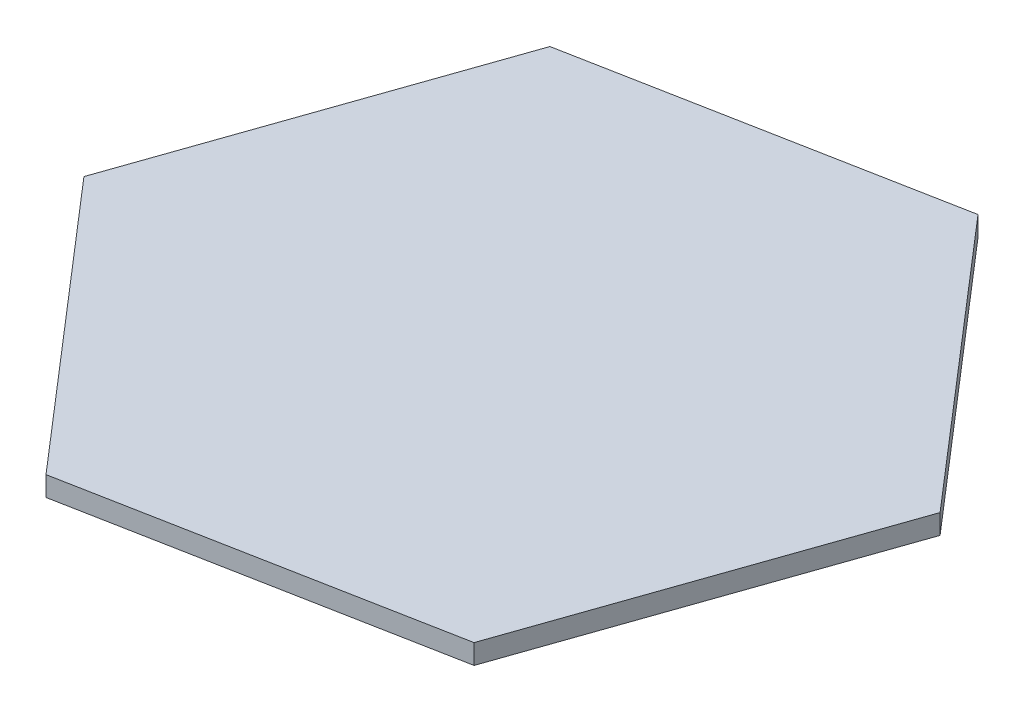
SolidWorks part; units mm, degrees
ref_plane "Front Plane" through (0, 0, 0) normal (0, 0, 1) x (1, 0, 0)
ref_plane "Top Plane" through (0, 0, 0) normal (0, 1, 0) x (1, 0, 0)
ref_plane "Right Plane" through (0, 0, 0) normal (1, 0, 0) x (0, 0, -1)
sketch "Sketch1" plane through (0, 0, 0) normal (0, 1, 0) x (1, 0, 0)
  line L1 (120.7144, -139.8592) -> (181.4788, 34.6121)
  line L2 (181.4788, 34.6121) -> (60.7644, 174.4713)
  line L3 (60.7644, 174.4713) -> (-120.7144, 139.8592)
  line L4 (-120.7144, 139.8592) -> (-181.4788, -34.6121)
  line L5 (-181.4788, -34.6121) -> (-60.7644, -174.4713)
  line L6 (-60.7644, -174.4713) -> (120.7144, -139.8592)
  line L11 (-100, 100) -> (100, -100) construction
  line L12 (-100, -100) -> (100, 100) construction
  circle A0 centre (0, 0) radius 159.9982 construction
  dimension "D3" = 184.75
extrude "Boss-Extrude2" add sketch "Sketch1" along normal blind 10
